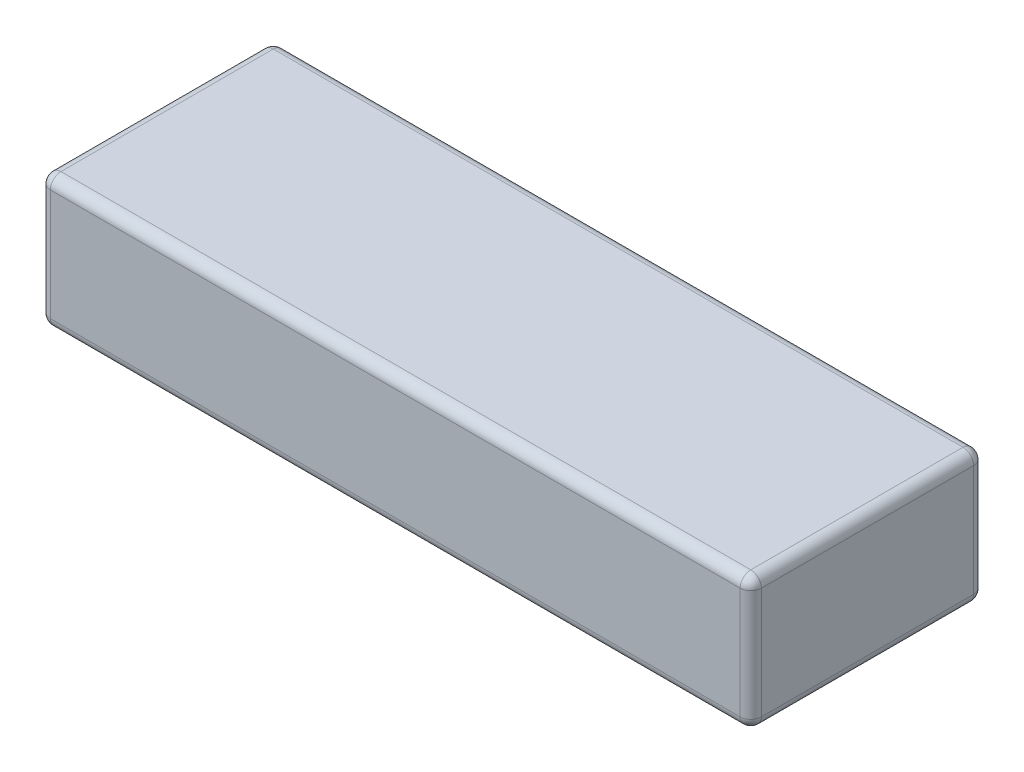
SolidWorks part; units mm, degrees
ref_plane "Front Plane" through (0, 0, 0) normal (0, 0, 1) x (1, 0, 0)
ref_plane "Top Plane" through (0, 0, 0) normal (0, 1, 0) x (1, 0, 0)
ref_plane "Right Plane" through (0, 0, 0) normal (1, 0, 0) x (0, 0, -1)
other "Center of Mass"
sketch "Sketch1" plane through (0, 0, 0) normal (0, 1, 0) x (1, 0, 0)
  line L1 (-67, -22) -> (67, -22)
  line L2 (-67, -22) -> (-67, 22)
  line L3 (-67, 22) -> (67, 22)
  line L4 (67, -22) -> (67, 22)
  line L5 (-67, -22) -> (67, 22) construction
  line L6 (-67, 22) -> (67, -22) construction
  point P0 (0, 0)
  dimension "D1" = 134
  dimension "D2" = 44
extrude "Boss-Extrude1" add sketch "Sketch1" along normal blind 25
fillet "Fillet1" radius 2 12 edges at (67, 12.5, -22) (-67, 12.5, -22) (-67, 12.5, 22) (67, 12.5, 22) (0, 25, 22) (-67, 25, 0) (0, 25, -22) (67, 25, 0) (0, 0, 22) (-67, 0, 0) (0, 0, -22) (67, 0, 0)
